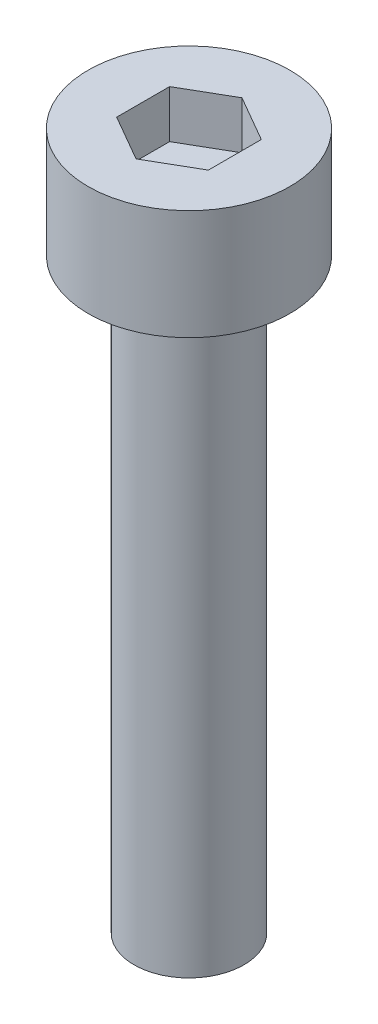
SolidWorks part; units mm, degrees
material "AISI Type A2 Tool Steel"
ref_plane "Front" through (0, 0, 0) normal (0, 0, 1) x (1, 0, 0)
ref_plane "Top" through (0, 0, 0) normal (0, 1, 0) x (1, 0, 0)
ref_plane "Right" through (0, 0, 0) normal (1, 0, 0) x (0, 0, -1)
sketch "Sketch1" plane through (0, 0, 0) normal (0, 1, 0) x (1, 0, 0)
  circle A0 centre (0, 0) radius 2.75
  dimension "D1" = 5.5
extrude "Boss-Extrude1" add sketch "Sketch1" along normal blind 3
sketch "Sketch2" plane through (0, 3, 0) normal (0, 1, 0) x (1, 0, 0)
  line L1 (0, 1.4434) -> (-1.25, 0.7217)
  line L2 (-1.25, 0.7217) -> (-1.25, -0.7217)
  line L3 (-1.25, -0.7217) -> (0, -1.4434)
  line L4 (0, -1.4434) -> (1.25, -0.7217)
  line L5 (1.25, -0.7217) -> (1.25, 0.7217)
  line L6 (1.25, 0.7217) -> (0, 1.4434)
  circle A0 centre (0, 0) radius 1.25 construction
  dimension "D1" = 2.5
extrude "Cut-Extrude1" cut sketch "Sketch2" against normal blind 1.3
sketch "Sketch3" plane through (0, 0, 0) normal (0, -1, 0) x (1, 0, 0)
  circle A0 centre (0, 0) radius 1.5
  dimension "D1" = 3
extrude "Boss-Extrude2" add sketch "Sketch3" along normal blind 16
equation "\"`2.40\"=2.8"
